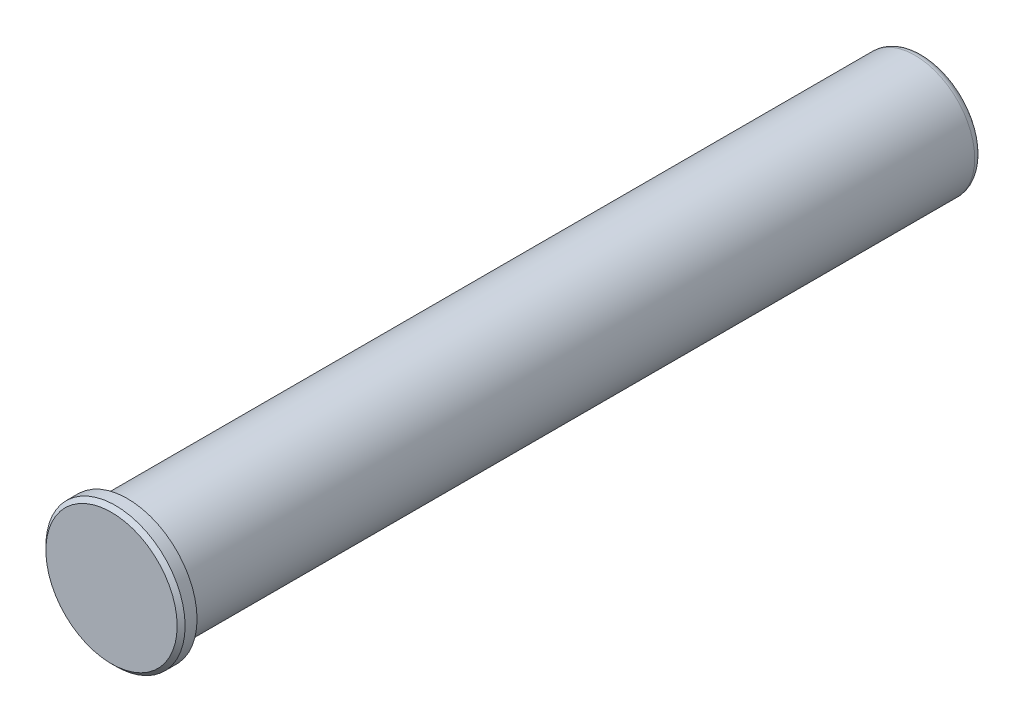
SolidWorks part; units mm, degrees
material "1.0037 (S235JR)"
ref_plane "Ön Düzlem" through (0, 0, 0) normal (0, 0, 1) x (1, 0, 0)
ref_plane "Üst Düzlem" through (0, 0, 0) normal (0, 1, 0) x (1, 0, 0)
ref_plane "Sağ Düzlem" through (0, 0, 0) normal (1, 0, 0) x (0, 0, -1)
sketch "Çizim1" plane through (0, 0, 0) normal (0, 0, 1) x (1, 0, 0)
  circle A0 centre (0, 0) radius 15
  dimension "D1" = 30
extrude "Yükseklik-Ekstrüzyon1" add sketch "Çizim1" along normal blind 200
sketch "Çizim2" plane through (0, 0, 200) normal (0, 0, 1) x (1, 0, 0)
  circle A0 centre (0, 0) radius 17.5
  dimension "D1" = 35
extrude "Yükseklik-Ekstrüzyon2" add sketch "Çizim2" along normal blind 4
fillet "Radyus1" radius 0.5 1 edges at (15, 0, 200)
chamfer "Pah1" distance 1 angle 45 1 edges at (17.5, 0, 204)
fillet "Radyus2" radius 2 1 edges at (15, 0, 0)
